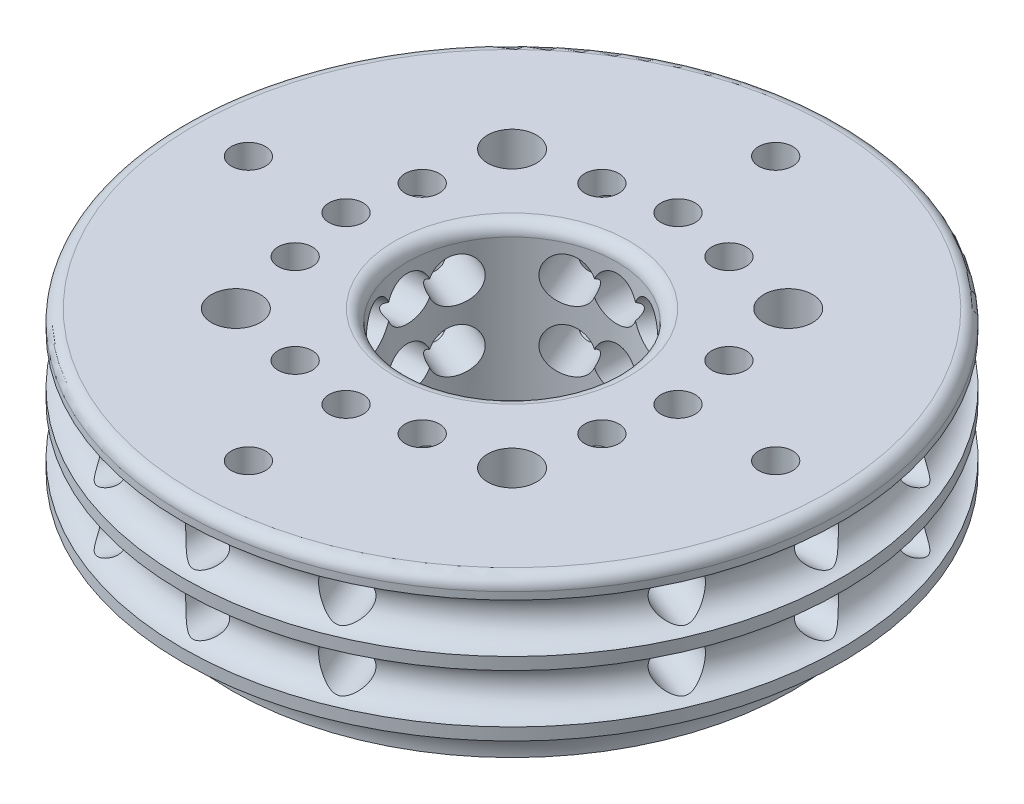
SolidWorks part; units mm, degrees
ref_plane "Front Plane" through (0, 0, 0) normal (0, 0, 1) x (1, 0, 0)
ref_plane "Top Plane" through (0, 0, 0) normal (0, 1, 0) x (1, 0, 0)
ref_plane "Right Plane" through (0, 0, 0) normal (1, 0, 0) x (0, 0, -1)
sketch "Sketch1" plane through (0, 0, 0) normal (0, 1, 0) x (1, 0, 0)
  line L0 (9.5459, -9.5459) -> (-9.5459, 9.5459) construction
  line L1 (0, -13.5) -> (0, 13.5) construction
  circle A0 centre (0, 0) radius 4.3
  circle A1 centre (0, 0) radius 13.5
  circle A2 centre (-5.6569, 5.6569) radius 1
  circle A3 centre (5.6569, 5.6569) radius 1
  circle A4 centre (5.6569, -5.6569) radius 1
  circle A5 centre (-5.6569, -5.6569) radius 1
  point P15 (0, 0)
  dimension "D1" = 8.6
  dimension "D2" = 27
  dimension "D3" = 2
  dimension "D4" = 8
  dimension "D6" = 45
  dimension "D5" = 4
extrude "Boss-Extrude1" add sketch "Sketch1" along normal blind 7
sketch "Sketch2" plane through (0, 7, 0) normal (0, 1, 0) x (1, 0, 0)
  circle A0 centre (0, 0) radius 5
  dimension "D2" = 10
extrude "Boss-Extrude2" add sketch "Sketch2" against normal blind 3.5
sketch "Sketch3" plane through (0, 0, 0) normal (0, -1, 0) x (1, 0, 0)
  circle A0 centre (0, 0) radius 10.325
  dimension "D1" = 20.65
extrude "Cut-Extrude1" cut sketch "Sketch3" against normal blind 1.5
ref_plane "Plane1" through (0, 3.5, 0) normal (0, 1, 0) x (1, 0, 0)
sketch "Sketch5" plane through (0, 3.5, 0) normal (0, 1, 0) x (1, 0, 0)
  circle A0 centre (0, 0) radius 13.5
sweep "Cut-Sweep1" cut path "Sketch5" circular profile diameter 2 parameters "D3"=2
ref_plane "Plane2" through (0, 6, 0) normal (0, 1, 0) x (1, 0, 0)
sketch "Sketch99" plane through (0, 6, 0) normal (0, 1, 0) x (1, 0, 0)
  circle A0 centre (0, 0) radius 13.5
  circle A1 centre (0, 0) radius 13.5 construction
sweep "Cut-Sweep2" cut path "Sketch99" circular profile diameter 2 parameters "D3"=2
chamfer "Chamfer1" distance 2 angle 45 1 edges at (0, 0, 13.5)
sketch "Sketch40" plane through (0, 7, 0) normal (0, 1, 0) x (1, 0, 0)
  circle A0 centre (-5.6569, -5.6569) radius 2.55
  circle A1 centre (-5.6569, 5.6569) radius 2.55
  circle A2 centre (5.6569, 5.6569) radius 2.55
  circle A3 centre (5.6569, -5.6569) radius 2.55
  dimension "D1" = 5.1
extrude "Cut-Extrude3" cut sketch "Sketch40" against normal blind 2
sketch "Sketch100" plane through (0, 0, 0) normal (1, 0, 0) x (0, 0, -1)
  line L0 (-11.5, 0) -> (11.5, 0) construction
  circle A0 centre (-13.5, 0) radius 2
sketch "Sketch101" plane through (0, 0, 0) normal (0, 1, 0) x (1, 0, 0)
  circle A0 centre (0, 0) radius 13.5
sweep "Cut-Sweep3" cut profiles "Sketch100" path "Sketch101"
sketch "Sketch108" plane through (0, 5, 0) normal (0, 1, 0) x (1, 0, 0)
  circle A0 centre (-5.6569, 5.6569) radius 2.55 construction
  circle A1 centre (-5.6569, -5.6569) radius 2.55 construction
  circle A2 centre (5.6569, -5.6569) radius 2.55 construction
  circle A3 centre (5.6569, 5.6569) radius 2.55 construction
  circle A4 centre (-5.6569, 5.6569) radius 2.55
  circle A5 centre (-5.6569, -5.6569) radius 2.55
  circle A6 centre (5.6569, -5.6569) radius 2.55
  circle A7 centre (5.6569, 5.6569) radius 2.55
  circle A8 centre (5.6569, 5.6569) radius 1
  circle A9 centre (5.6569, -5.6569) radius 1
  circle A10 centre (-5.6569, -5.6569) radius 1
  circle A11 centre (-5.6569, 5.6569) radius 1
extrude "Boss-Extrude3" add sketch "Sketch108" along normal blind 2.8
sketch "Sketch109" plane through (0, 7, 0) normal (0, 1, 0) x (1, 0, 0)
  circle A0 centre (0, 0) radius 13.5
  circle A1 centre (0, 0) radius 4.3
  circle A2 centre (5.6569, -5.6569) radius 2.55
  circle A3 centre (-5.6569, -5.6569) radius 2.55
  circle A4 centre (-5.6569, 5.6569) radius 2.55
  circle A5 centre (5.6569, 5.6569) radius 2.55
  circle A6 centre (5.6569, -5.6569) radius 2.55 construction
  circle A7 centre (-5.6569, -5.6569) radius 2.55 construction
  circle A8 centre (-5.6569, 5.6569) radius 2.55 construction
  circle A9 centre (5.6569, 5.6569) radius 2.55 construction
  circle A10 centre (0, 0) radius 13.5 construction
extrude "Boss-Extrude4" add sketch "Sketch109" along normal up to surface (0.8 mm away) up to face at (5.6569, 7.8, 8.2069)
sketch "Sketch164" plane through (0, 7, 0) normal (0, 1, 0) x (1, 0, 0)
  circle A0 centre (0, 0) radius 4.3
extrude "Cut-Extrude6" cut sketch "Sketch164" against normal through all both and the other way through all
sketch "Sketch165" plane through (0, 3.5, 0) normal (0, 1, 0) x (1, 0, 0)
  line L0 (13.5, 0) -> (-13.5, 0) construction
  line L1 (0, -13.5) -> (0, 13.5) construction
  line L2 (9.5459, -9.5459) -> (-9.5459, 9.5459) construction
  line L3 (-9.5459, -9.5459) -> (9.5459, 9.5459) construction
  line L4 (5.1662, -12.4724) -> (-5.1662, 12.4724) construction
  line L5 (12.4724, 5.1662) -> (-12.4724, -5.1662) construction
  line L6 (12.4724, -5.1662) -> (-12.4724, 5.1662) construction
  line L7 (-5.1662, -12.4724) -> (5.1662, 12.4724) construction
  circle A0 centre (0, 0) radius 13.5 construction
  dimension "D1" = 45
  dimension "D2" = 45
  dimension "D3" = 22.5
  dimension "D4" = 22.5
  dimension "D5" = 22.5
  dimension "D6" = 22.5
ref_plane "Plane3" through (0, 4.75, 0) normal (0, 1, 0) x (1, 0, 0)
sketch "Sketch167" plane through (0, 3.5, 0) normal (0, 1, 0) x (1, 0, 0)
  line L0 (0, -13.5) -> (0, 13.5)
sweep "Cut-Sweep4" cut path "Sketch167" circular profile diameter 1.8 parameters "D3"=1.8
sketch "Sketch208" plane through (0, 3.5, 0) normal (0, 1, 0) x (1, 0, 0)
  line L0 (5.1662, 12.4724) -> (-5.1662, -12.4724)
sweep "Cut-Sweep5" cut path "Sketch208" circular profile diameter 1.8 parameters "D3"=1.8
sketch "Sketch221" plane through (0, 3.5, 0) normal (0, 1, 0) x (1, 0, 0)
  line L0 (-12.4724, -5.1662) -> (12.4724, 5.1662)
sweep "Cut-Sweep6" cut path "Sketch221" circular profile diameter 1.8 parameters "D3"=1.8
sketch "Sketch234" plane through (0, 3.5, 0) normal (0, 1, 0) x (1, 0, 0)
  line L0 (13.5, 0) -> (-13.5, 0)
sweep "Cut-Sweep7" cut path "Sketch234" circular profile diameter 1.8 parameters "D3"=1.8
sketch "Sketch247" plane through (0, 3.5, 0) normal (0, 1, 0) x (1, 0, 0)
  line L0 (12.4724, -5.1662) -> (-12.4724, 5.1662)
sweep "Cut-Sweep8" cut path "Sketch247" circular profile diameter 1.8 parameters "D3"=1.8
sketch "Sketch260" plane through (0, 3.5, 0) normal (0, 1, 0) x (1, 0, 0)
  line L0 (5.1662, -12.4724) -> (-5.1662, 12.4724)
sweep "Cut-Sweep9" cut path "Sketch260" circular profile diameter 1.8 parameters "D3"=1.8
mirror "Mirror1" about plane through (0, 4.75, 0) normal (0, 1, 0) of "Cut-Sweep9", "Cut-Sweep8", "Cut-Sweep7", "Cut-Sweep6", "Cut-Sweep5", "Cut-Sweep4"
sketch "Sketch285" plane through (0, 7.8, 0) normal (0, 1, 0) x (1, 0, 0)
  line L0 (0, -13.5) -> (0, 13.5) construction
  circle A0 centre (0, -6.8) radius 0.7
  circle A1 centre (-2.6022, -6.2824) radius 0.7
  circle A3 centre (-6.2824, -2.6022) radius 0.7
  circle A4 centre (-6.8, 0) radius 0.7
  circle A5 centre (-6.2824, 2.6022) radius 0.7
  circle A7 centre (-2.6022, 6.2824) radius 0.7
  circle A8 centre (0, 6.8) radius 0.7
  circle A9 centre (2.6022, 6.2824) radius 0.7
  circle A11 centre (6.2824, 2.6022) radius 0.7
  circle A12 centre (6.8, 0) radius 0.7
  circle A13 centre (6.2824, -2.6022) radius 0.7
  circle A15 centre (2.6022, -6.2824) radius 0.7
  circle A16 centre (4.8083, -4.8083) radius 0.7 [skipped]
  circle A17 centre (-4.8083, -4.8083) radius 0.7 [skipped]
  circle A18 centre (-4.8083, 4.8083) radius 0.7 [skipped]
  circle A19 centre (4.8083, 4.8083) radius 0.7 [skipped]
  point P37 (0, 0)
  dimension "D1" = 1.4
  dimension "D2" = 6.8
  dimension "D3" = 16
extrude "Cut-Extrude7" cut sketch "Sketch285" against normal blind 5.5
fillet "Fillet1" radius 0.5 2 edges at (0, 7.8, 4.3) (0, 7.8, 13.5)
sketch "Sketch286" plane through (0, 7.8, 0) normal (0, 1, 0) x (1, 0, 0)
  line L0 (0, 13) -> (0, 0) construction
  circle A0 centre (0, 0) radius 13 construction
  circle A1 centre (0, 10.8) radius 0.7
  circle A2 centre (0, 6.8) radius 0.7 construction
  circle A3 centre (10.8, 0) radius 0.7
  circle A4 centre (0, -10.8) radius 0.7
  circle A5 centre (-10.8, 0) radius 0.7
  point P18 (0, 0)
  dimension "D1" = 1.4
  dimension "D2" = 4
  dimension "D3" = 4
extrude "Cut-Extrude8" cut sketch "Sketch286" against normal blind 5
